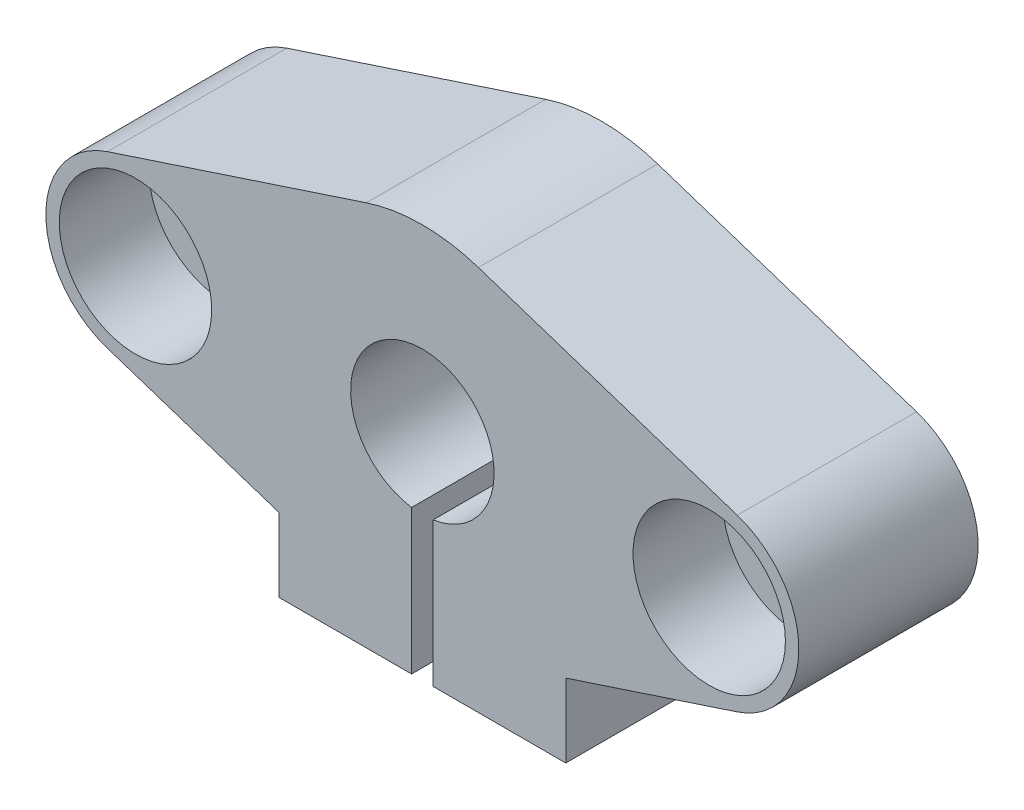
SolidWorks part; units mm, degrees
ref_plane "前视基准面" through (0, 0, 0) normal (0, 0, 1) x (1, 0, 0)
ref_plane "上视基准面" through (0, 0, 0) normal (0, 1, 0) x (1, 0, 0)
ref_plane "右视基准面" through (0, 0, 0) normal (1, 0, 0) x (0, 0, -1)
sketch "草图1" plane through (0, 0, 0) normal (0, 0, 1) x (1, 0, 0)
  circle A0 centre (0, 0) radius 4
  circle A1 centre (0, 0) radius 10
  dimension "D1" = 8
  dimension "D2" = 20
extrude "凸台-拉伸1" add sketch "草图1" along normal blind 10
sketch "草图2" plane through (0, 0, 0) normal (0, 0, 1) x (1, 0, 0)
  line L1 (-21.5, 10) -> (21.5, 10)
  line L2 (-21.5, 10) -> (-21.5, -10)
  line L3 (-21.5, -10) -> (21.5, -10)
  line L4 (21.5, 10) -> (21.5, -10)
  line L5 (-21.5, 10) -> (21.5, -10) construction
  line L6 (-21.5, -10) -> (21.5, 10) construction
  circle A0 centre (0, 0) radius 10 construction
  circle A1 centre (0, 0) radius 10
  point P0 (0, 0)
  dimension "D1" = 43
  dimension "D2" = 20
extrude "凸台-拉伸2" add sketch "草图2" along normal blind 5 contours A1 L1 L2 L3 | A1 L3 L4 L1
sketch "草图4" plane through (0, 0, 0) normal (0, 0, 1) x (1, 0, 0)
  line L0 (0, 0) -> (0, 11.7856) construction
  line L1 (0, 0) -> (8.9774, 0) construction
  circle A0 centre (-16, 0) radius 2.75
  circle A1 centre (16, 0) radius 2.75
  dimension "D1" = 5.5
  dimension "D2" = 16
extrude "切除-拉伸6" cut sketch "草图4" along normal blind 5
sketch "草图3" plane through (0, 0, 0) normal (0, 0, 1) x (1, 0, 0)
  line L0 (0, 0) -> (15.1245, 0) construction
  line L1 (0, 0) -> (0, 7.4075) construction
  line L2 (-17.5625, 4.7496) -> (-3.125, 9.4992)
  line L3 (-21.5, -10) -> (-21.5, 10)
  line L5 (-17.5625, -4.7496) -> (-3.125, -9.4992)
  line L6 (21.5, -10) -> (21.5, 10)
  line L7 (-21.5, -10) -> (21.5, -10)
  line L9 (-21.5, 10) -> (21.5, 10)
  line L11 (17.5625, 4.7496) -> (3.125, 9.4992)
  line L13 (17.5625, -4.7496) -> (3.125, -9.4992)
  arc A0 (0, 10) -> (0, -10) centre (0, 0) ccw construction
  circle A1 centre (-16, 0) radius 5
  arc A2 (0, 10) -> (-3.125, 9.4992) centre (0, 0) ccw
  arc A3 (0, -10) -> (0, 10) centre (0, 0) ccw construction
  arc A4 (0, -10) -> (3.125, -9.4992) centre (0, 0) ccw
  arc A5 (-3.125, -9.4992) -> (0, -10) centre (0, 0) ccw
  arc A6 (3.125, 9.4992) -> (0, 10) centre (0, 0) ccw
  circle A7 centre (16, 0) radius 5
  point P23 (0, 10)
  point P28 (0, -10)
  dimension "D2" = 10
  dimension "D3" = 10
extrude "切除-拉伸5" cut sketch "草图3" along normal blind 5
sketch "草图5" plane through (0, 0, 0) normal (0, 0, 1) x (1, 0, 0)
  line L0 (-26.9323, 0) -> (-13.5767, 0) construction
  line L1 (0, 14.5275) -> (0, 4.7098) construction
  line L2 (-9.5523, -12) -> (9.9061, -12) construction
  line L3 (-8, -6) -> (-8, -12)
  line L5 (-8, -12) -> (8, -12)
  line L7 (0, -12) -> (0, -10)
  line L8 (8, -6) -> (8, -12)
  circle A0 centre (0, 0) radius 10 construction
  arc A1 (-8, -6) -> (8, -6) centre (0, 0) ccw
  arc A2 (-3.125, 9.4992) -> (-3.125, -9.4992) centre (0, 0) ccw construction
  dimension "D1" = 12
  dimension "D2" = 8
extrude "凸台-拉伸3" add sketch "草图5" along normal blind 10 contours A1 L8 L5 L3
sketch "草图6" plane through (0, 0, 0) normal (0, 0, 1) x (1, 0, 0)
  line L0 (0, 1008) -> (0, 4) construction
  line L1 (-8, -12) -> (8, -12) construction
  line L2 (-0.6, -12) -> (0.6, -12)
  line L3 (-0.6, -3.9547) -> (-0.6, -12)
  line L4 (0.6, -3.9547) -> (0.6, -12)
  line L5 (0, -4) -> (0, -15.0853) construction
  circle A0 centre (0, 0) radius 4 construction
  arc A1 (-0.6, -3.9547) -> (0.6, -3.9547) centre (0, 0) ccw
  dimension "D1" = 0.6
extrude "切除-拉伸8" cut sketch "草图6" along normal through all
sketch "草图7" plane through (0, 0, 5) normal (0, 0, 1) x (1, 0, 0)
  line L4 (-17.5625, -4.7496) -> (-8, -7.8954)
  line L5 (-8, -7.8954) -> (-8, -6)
  line L6 (-3.125, 9.4992) -> (-17.5625, 4.7496)
  line L8 (-17.5625, -4.7496) -> (-8, -7.8954)
  line L9 (-8, -7.8954) -> (-8, -6)
  line L10 (-3.125, 9.4992) -> (-17.5625, 4.7496)
  line L12 (8, -6) -> (8, -7.8954)
  line L13 (8, -7.8954) -> (17.5625, -4.7496)
  line L15 (17.5625, 4.7496) -> (3.125, 9.4992)
  line L16 (8, -6) -> (8, -7.8954)
  line L17 (8, -7.8954) -> (17.5625, -4.7496)
  line L19 (17.5625, 4.7496) -> (3.125, 9.4992)
  circle A0 centre (-16, 0) radius 4.25
  arc A1 (-3.125, 9.4992) -> (-8, -6) centre (0, 0) ccw
  arc A2 (-3.125, 9.4992) -> (-8, -6) centre (0, 0) ccw
  arc A3 (8, -6) -> (3.125, 9.4992) centre (0, 0) ccw
  arc A4 (8, -6) -> (3.125, 9.4992) centre (0, 0) ccw
  circle A5 centre (16, 0) radius 4.25
  arc A8 (-17.5625, 4.7496) -> (-17.5625, -4.7496) centre (-16, 0) ccw
  arc A9 (-17.5625, 4.7496) -> (-17.5625, -4.7496) centre (-16, 0) ccw
  arc A10 (17.5625, -4.7496) -> (17.5625, 4.7496) centre (16, 0) ccw
  arc A11 (17.5625, -4.7496) -> (17.5625, 4.7496) centre (16, 0) ccw
  dimension "D3" = 8.5
  dimension "D4" = 8.5
  dimension "D1" = 0
  dimension "D2" = 0
extrude "凸台-拉伸4" add sketch "草图7" along normal blind 5
